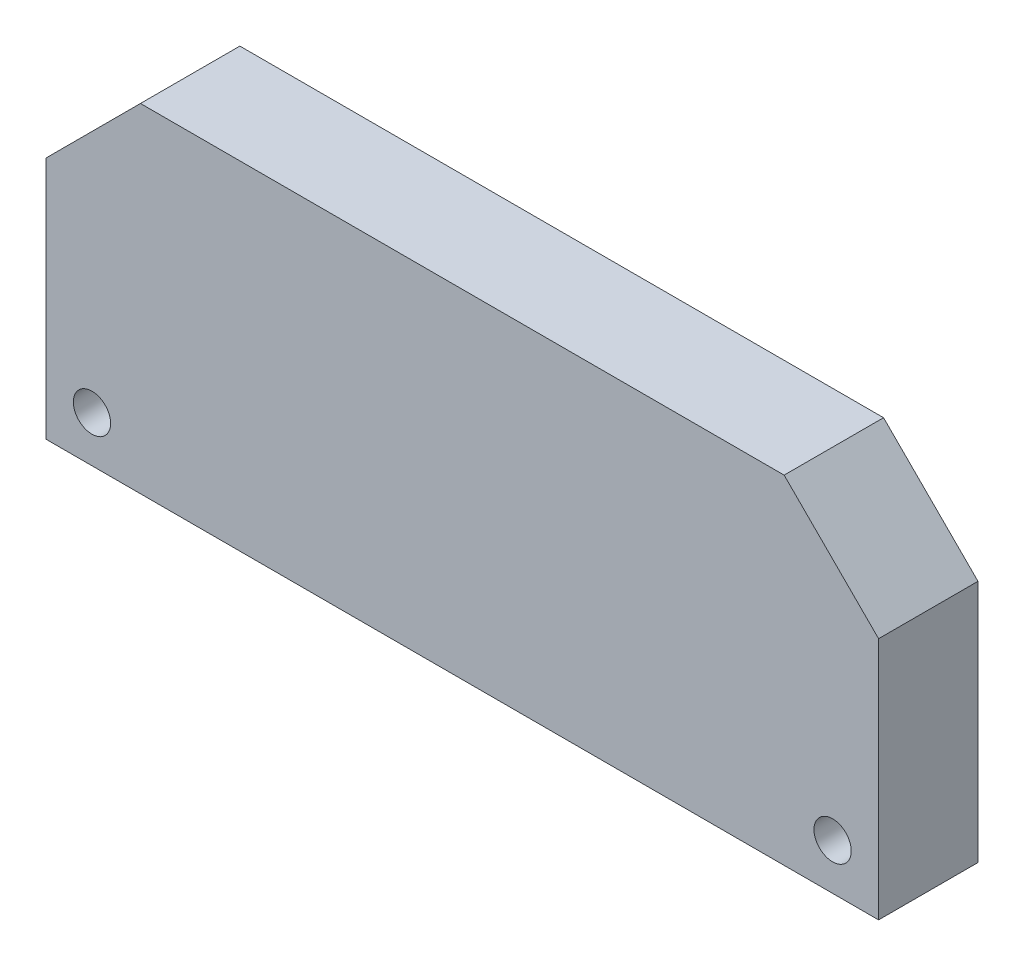
SolidWorks part; units mm, degrees
ref_plane "Ön Düzlem" through (0, 0, 0) normal (0, 0, 1) x (1, 0, 0)
ref_plane "Üst Düzlem" through (0, 0, 0) normal (0, 1, 0) x (1, 0, 0)
ref_plane "Sağ Düzlem" through (0, 0, 0) normal (1, 0, 0) x (0, 0, -1)
sketch "Sketch1" plane through (0, 0, 0) normal (0, 0, 1) x (1, 0, 0)
  line L1 (-33.5, 13.6) -> (33.5, 13.6)
  line L2 (-33.5, 13.6) -> (-33.5, -13.6)
  line L3 (-33.5, -13.6) -> (33.5, -13.6)
  line L4 (33.5, 13.6) -> (33.5, -13.6)
  line L5 (-33.5, 13.6) -> (33.5, -13.6) construction
  line L6 (-33.5, -13.6) -> (33.5, 13.6) construction
  point P0 (0, 0)
  dimension "D1" = 27.2
  dimension "D2" = 67
extrude "Boss-Extrude1" add sketch "Sketch1" along normal blind 8
sketch "Sketch3" plane through (0, 0, 8) normal (0, 0, 1) x (1, 0, 0)
  line L0 (-33.5, -13.6) -> (33.5, -13.6) construction
  line L1 (33.5, -13.6) -> (33.5, 13.6) construction
  line L2 (-33.5, 13.6) -> (-33.5, -13.6) construction
  circle A0 centre (29.8, -9.9) radius 1.5
  circle A1 centre (-29.8, -9.9) radius 1.5
  point P8 (0, 0)
  dimension "D3" = 3
  dimension "D4" = 3.7
  dimension "D1" = 3.7
  dimension "D2" = 3.7
  dimension "D5" = 3.7
  dimension "D6" = 59.6
extrude "Cut-Extrude1" cut sketch "Sketch3" against normal blind 8
chamfer "Chamfer1" distance 7.6 angle 45 2 edges at (33.5, 13.6, 4) (-33.5, 13.6, 4)
